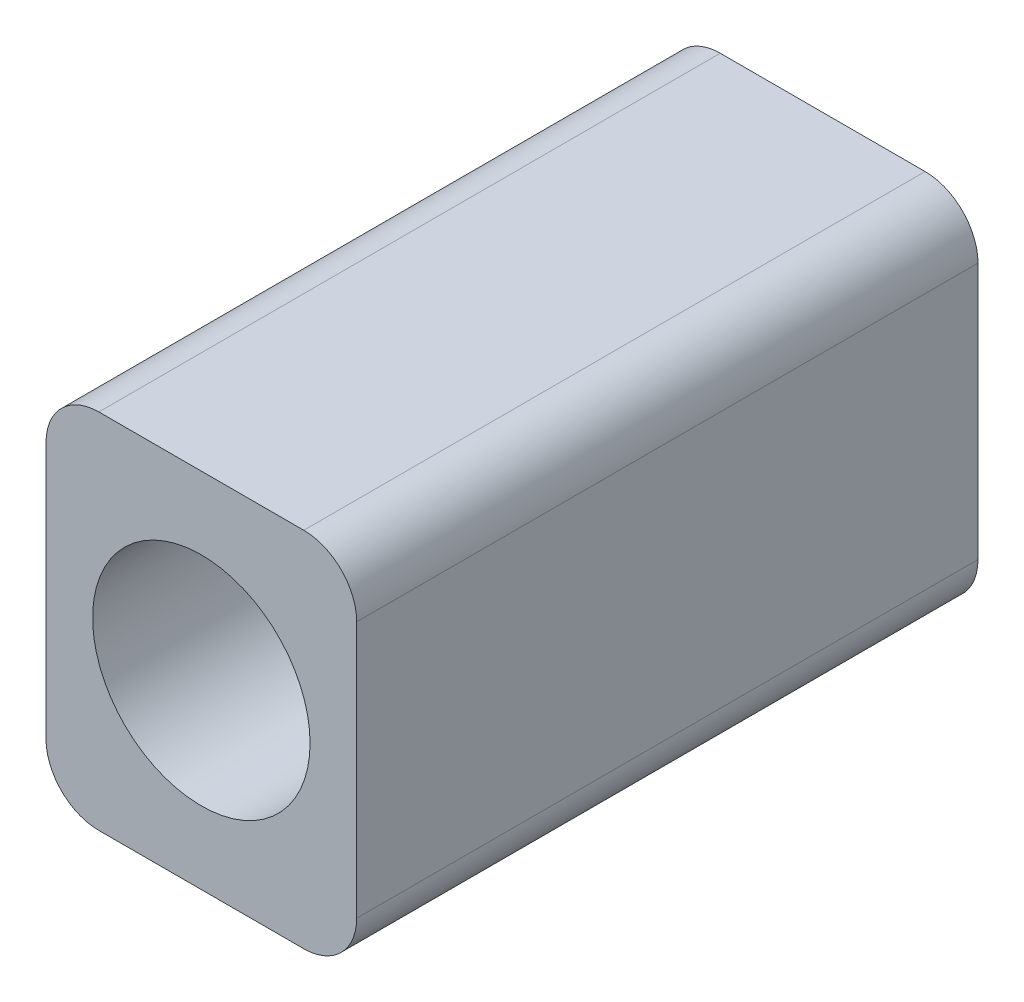
SolidWorks part; units mm, degrees
ref_plane "Front Plane" through (0, 0, 0) normal (0, 0, 1) x (1, 0, 0)
ref_plane "Top Plane" through (0, 0, 0) normal (0, 1, 0) x (1, 0, 0)
ref_plane "Right Plane" through (0, 0, 0) normal (1, 0, 0) x (0, 0, -1)
sketch "Sketch1" plane through (0, 0, 0) normal (0, 0, 1) x (1, 0, 0)
  line L1 (1.0212, 0) -> (4.9788, 0)
  line L2 (0, 1.0212) -> (0, 5.9788)
  line L3 (1.0212, 7) -> (4.9788, 7)
  line L4 (6, 1.0212) -> (6, 5.9788)
  line L5 (0, 0) -> (6, 7) construction
  line L6 (0, 7) -> (6, 0) construction
  arc A0 (1.0212, 0) -> (0, 1.0212) centre (1.0212, 1.0212) cw
  arc A1 (6, 1.0212) -> (4.9788, 0) centre (4.9788, 1.0212) cw
  arc A2 (6, 5.9788) -> (4.9788, 7) centre (4.9788, 5.9788) ccw
  arc A3 (0, 5.9788) -> (1.0212, 7) centre (1.0212, 5.9788) cw
  point P4 (3, 3.5)
  dimension "D3" = 1.0212
  dimension "D1" = 6
  dimension "D2" = 7
extrude "Boss-Extrude1" add sketch "Sketch1" along normal blind 12
sketch "Sketch2" plane through (0, 0, 12) normal (0, 0, 1) x (1, 0, 0)
  line L2 (3, 3.5) -> (0, 3.5) construction
  line L3 (0, 5.9788) -> (0, 1.0212) construction
  line L4 (3, 3.5) -> (3, 7) construction
  line L5 (4.9788, 7) -> (1.0212, 7) construction
  circle A0 centre (3, 3.5) radius 2.1
  dimension "D1" = 4.2
extrude "Cut-Extrude1" cut sketch "Sketch2" against normal blind 8
